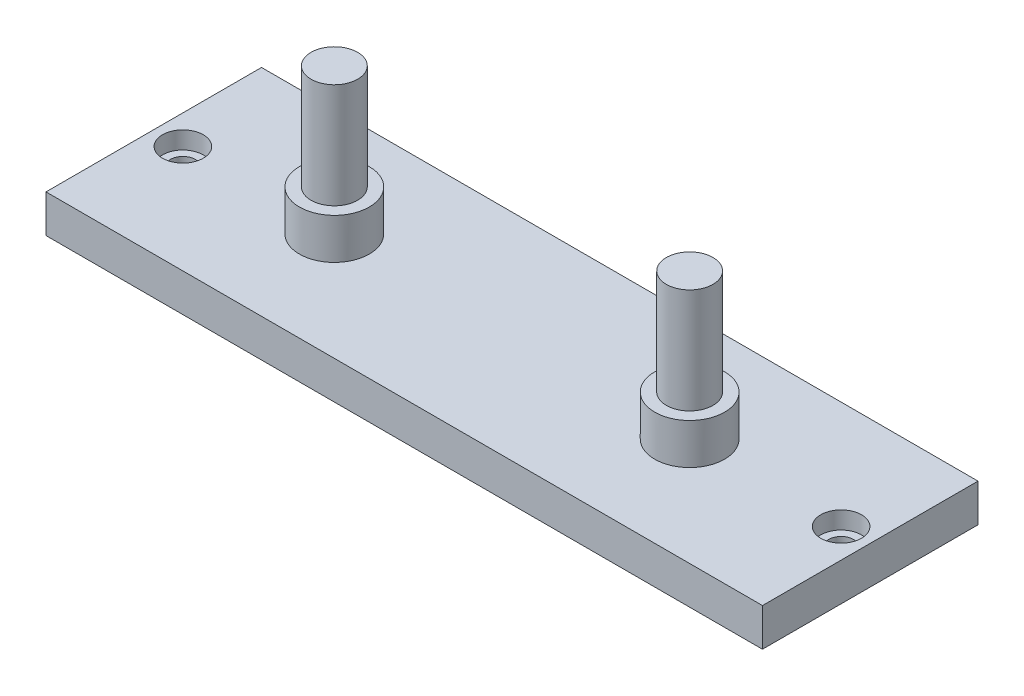
SolidWorks part; units mm, degrees
ref_plane "Front" through (0, 0, 0) normal (0, 0, 1) x (1, 0, 0)
ref_plane "Top" through (0, 0, 0) normal (0, 1, 0) x (1, 0, 0)
ref_plane "Right" through (0, 0, 0) normal (1, 0, 0) x (0, 0, -1)
sketch "Sketch1" plane through (0, 0, 0) normal (0, 1, 0) x (1, 0, 0)
  line L1 (0, 0) -> (123, 0)
  line L2 (0, 0) -> (0, 37)
  line L3 (0, 37) -> (123, 37)
  line L4 (123, 0) -> (123, 37)
  dimension "D1" = 37
  dimension "D2" = 123
extrude "Boss-Extrude1" add sketch "Sketch1" along normal blind 6.5
hole_wizard "CBORE for M4 Hex Head Machine Screw1" positions "Sketch6" profile "Sketch5" counterbore size "M4" standard "ANSI Metric" end condition through all
sketch "Sketch6" plane through (0, 6.5, 0) normal (0, 1, 0) x (1, 0, 0)
  line L0 (0, 37) -> (0, 0) construction
  line L1 (123, 0) -> (123, 37) construction
  point P0 (5, 18.5)
  point P3 (118, 18.5)
  dimension "D1" = 5
  dimension "D2" = 5
sketch "Sketch5" plane through (5, 6.5, -18.5) normal (1, 0, 0) x (0, 0, 1)
  line L0 (0, 0) -> (0, 6.5)
  line L1 (0, 6.5) -> (2.15, 6.5)
  line L3 (2.15, 6.5) -> (2.15, 3)
  line L4 (2.15, 3) -> (3.5, 3)
  line L5 (3.5, 3) -> (3.5, 0)
  line L7 (3.5, 0) -> (0, 0)
  line L11 (0, -6.35) -> (0, 107.95) construction
  dimension "Thru Hole Dia." = 4.3
  dimension "Thru Hole Depth" = 6.5
  dimension "C'Bore Dia." = 7
  dimension "C'Bore Depth" = 3
sketch "Sketch7" plane through (0, 6.5, 0) normal (0, 1, 0) x (1, 0, 0)
  line L0 (92, 18.5) -> (31, 18.5) construction
  line L1 (0, 0) -> (123, 0) construction
  line L3 (123, 0) -> (123, 37) construction
  circle A0 centre (31, 18.5) radius 4
  circle A1 centre (92, 18.5) radius 4
  point P6 (61.5, 0)
  point P7 (61.5, 18.5)
  point P10 (123, 18.5)
  dimension "D1" = 8
  dimension "D2" = 61
extrude "Boss-Extrude2" add sketch "Sketch7" along normal blind 25
sketch "Sketch8" plane through (0, 6.5, 0) normal (0, 1, 0) x (1, 0, 0)
  circle A0 centre (31, 18.5) radius 6
  circle A1 centre (92, 18.5) radius 6
  dimension "D1" = 12
extrude "Boss-Extrude3" add sketch "Sketch8" along normal blind 7
